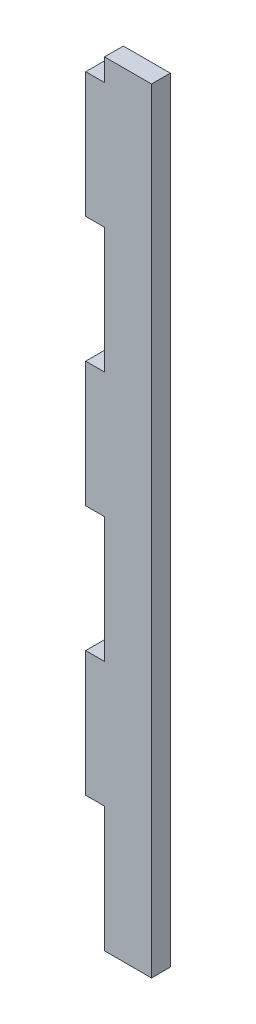
SolidWorks part; units mm, degrees
ref_plane "Face" through (0, 0, 0) normal (0, 0, 1) x (1, 0, 0)
ref_plane "Dessus" through (0, 0, 0) normal (0, 1, 0) x (1, 0, 0)
ref_plane "Droite" through (0, 0, 0) normal (1, 0, 0) x (0, 0, -1)
sketch "Esquisse1" plane through (0, 0, 0) normal (0, 0, 1) x (1, 0, 0)
  line L1 (15, 181.4099) -> (15, -65.6938)
  line L2 (15, -65.6938) -> (0, -65.6938)
  line L4 (-6, -25.692) -> (0, -25.692) construction
  line L8 (0, -65.6938) -> (0, -25.692) construction
  line L10 (-6, 14.3068) -> (-6, -25.692)
  line L12 (-6, 14.3068) -> (0, 14.3068) construction
  line L14 (-6, 14.3068) -> (0, 14.3068)
  line L15 (-6, 181.4099) -> (0, 181.4099) construction
  line L17 (0, -65.6938) -> (0, -25.692)
  line L18 (0, 14.3068) -> (0, 54.3086)
  line L19 (-6, 54.3086) -> (0, 54.3086)
  line L20 (-6, 94.3074) -> (-6, 54.3086)
  line L21 (-6, 94.3074) -> (0, 94.3074)
  line L22 (0, 94.3074) -> (0, 134.3092)
  line L23 (-6, 134.3092) -> (0, 134.3092)
  line L24 (-6, 174.308) -> (-6, 134.3092)
  line L25 (-6, 174.308) -> (0, 174.308)
  line L28 (0, 94.3074) -> (0, 134.3092) construction
  line L29 (0, 14.3068) -> (0, 54.3086) construction
  line L31 (0, 181.4099) -> (15, 181.4099)
  line L32 (0, 181.4099) -> (0, 174.308) construction
  line L34 (0, -25.692) -> (-6, -25.692)
  line L35 (0, 181.4099) -> (0, 174.308)
  line L36 (-6, 174.308) -> (-6, 134.3092) construction
  line L37 (-6, 134.3092) -> (-6, 94.3074) construction
  dimension "D2" = 15
  dimension "D3" = 3
extrude "Boss.-Extru.1" add sketch "Esquisse1" against normal blind 6
